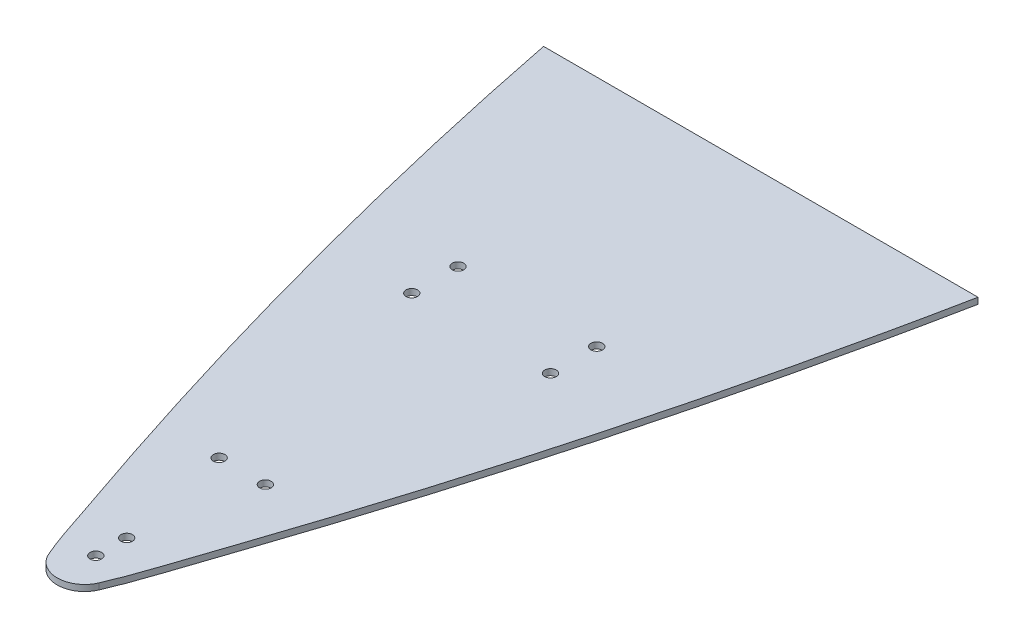
SolidWorks part; units mm, degrees
ref_plane "Front Plane" through (0, 0, 0) normal (0, 0, 1) x (1, 0, 0)
ref_plane "Top Plane" through (0, 0, 0) normal (0, 1, 0) x (1, 0, 0)
ref_plane "Right Plane" through (0, 0, 0) normal (1, 0, 0) x (0, 0, -1)
sketch "Sketch1" plane through (0, 0, 0) normal (0, 1, 0) x (1, 0, 0)
  line L0 (186.7062, -778.1024) -> (-171.2698, -778.1024)
  arc A0 (-12.9178, -1344.2422) -> (28.3543, -1344.2422) centre (7.7182, -1335.303) ccw
  spline S0 degree 3 poles (28.3543, -1344.2422) (38.1207, -1321.6964) (44.9392, -1298.0794) (60.8237, -1251.6716) (68.5445, -1228.3934) (91.0292, -1158.3687) (105.1224, -1111.4203) (144.7238, -969.7826) (167.5373, -874.3159) (186.7062, -778.1024) knots 0 0 0 0 0.125 0.125 0.25 0.25 0.5 0.5 1 1 1 1
  spline S1 degree 3 poles (-171.2698, -778.1024) (-159.7078, -836.1348) (-146.8189, -893.9188) (-132.6111, -951.3608) (-118.4033, -1008.8028) (-102.8733, -1065.9339) (-86.0456, -1122.6638) (-74.9901, -1159.9341) (-63.3713, -1197.0419) (-51.1942, -1233.961) (-45.1006, -1252.436) (-38.8668, -1270.8654) (-32.4946, -1289.2462) (-26.1208, -1307.6316) (-20.6525, -1326.3867) (-12.9178, -1344.2422) knots 0 0 0 0 0.177519 0.177519 0.177519 0.355038 0.355038 0.355038 0.471647 0.471647 0.471647 0.529995 0.529995 0.529995 0.588358 0.588358 0.588358 0.588358
extrude "Boss-Extrude1" add sketch "Sketch1" along normal blind 5.08 contours S1 A0 S0 L0
hole_wizard "3/8 (0.375) Diameter Hole1" positions "Sketch2" profile "Sketch3" hole size "3/8" standard "ANSI Inch" end condition through all
sketch "Sketch2" plane through (0, 5.08, 0) normal (0, 1, 0) x (1, 0, 0)
  line L0 (7.7182, -1357.792) -> (7.7182, -1326.042)
  line L1 (7.7182, -1326.042) -> (7.7182, -1300.642)
  arc A0 (-12.9178, -1344.2422) -> (28.3543, -1344.2422) centre (7.7182, -1335.303) ccw construction
  arc A1 (-12.9178, -1344.2422) -> (28.3543, -1344.2422) centre (7.7182, -1335.303) ccw
  point P0 (7.7182, -1326.042)
  point P2 (7.7182, -1300.642)
  dimension "D1" = 31.75
  dimension "D2" = 25.4
sketch "Sketch3" plane through (7.7182, 5.08, 1326.042) normal (1, 0, 0) x (0, 0, 1)
  line L0 (0, 0) -> (0, 5.08)
  line L1 (0, 5.08) -> (4.7625, 5.08)
  line L2 (4.7625, 5.08) -> (4.7625, 0)
  line L5 (4.7625, 0) -> (0, 0)
  line L11 (0, -6.35) -> (0, 107.95) construction
  dimension "Thru Hole Dia." = 9.525
  dimension "Thru Hole Depth" = 5.08
hole_wizard "3/8 (0.375) Diameter Hole2" positions "Sketch5" profile "Sketch6" hole size "3/8" standard "ANSI Inch" end condition through all
sketch "Sketch5" plane through (0, 5.08, 0) normal (0, 1, 0) x (1, 0, 0)
  line L0 (7.7182, -778.1024) -> (7.7182, -1357.792) construction
  line L1 (186.7062, -778.1024) -> (-171.2698, -778.1024) construction
  line L3 (-11.3318, -1205.392) -> (26.7682, -1205.392)
  line L10 (64.8682, -1008.542) -> (-49.4318, -1008.542)
  line L11 (64.8682, -1008.542) -> (64.8682, -970.442)
  line L12 (64.8682, -970.442) -> (-49.4318, -970.442)
  line L13 (-49.4318, -1008.542) -> (-49.4318, -970.442)
  line L14 (64.8682, -1008.542) -> (-49.4318, -970.442) construction
  line L15 (64.8682, -970.442) -> (-49.4318, -1008.542) construction
  arc A0 (-12.9178, -1344.2422) -> (28.3543, -1344.2422) centre (7.7182, -1335.303) ccw construction
  point P0 (-49.4318, -970.442)
  point P2 (-49.4318, -1008.542)
  point P4 (64.8682, -970.442)
  point P6 (64.8682, -1008.542)
  point P8 (-11.3318, -1205.392)
  point P10 (26.7682, -1205.392)
  point P27 (7.7182, -1205.392)
  point P87 (0, 0)
  point P88 (101.6367, -1007.948)
  point P89 (7.7182, -989.492)
  point P90 (64.8682, -989.492)
  dimension "D1" = 38.1
  dimension "D2" = 152.4
  dimension "D3" = 38.1
  dimension "D4" = 114.3
  dimension "D5" = 215.9
sketch "Sketch6" plane through (-49.4318, 5.08, 970.442) normal (1, 0, 0) x (0, 0, 1)
  line L0 (0, 0) -> (0, 5.08)
  line L1 (0, 5.08) -> (4.7625, 5.08)
  line L2 (4.7625, 5.08) -> (4.7625, 0)
  line L5 (4.7625, 0) -> (0, 0)
  line L11 (0, -6.35) -> (0, 107.95) construction
  dimension "Thru Hole Dia." = 9.525
  dimension "Thru Hole Depth" = 5.08
